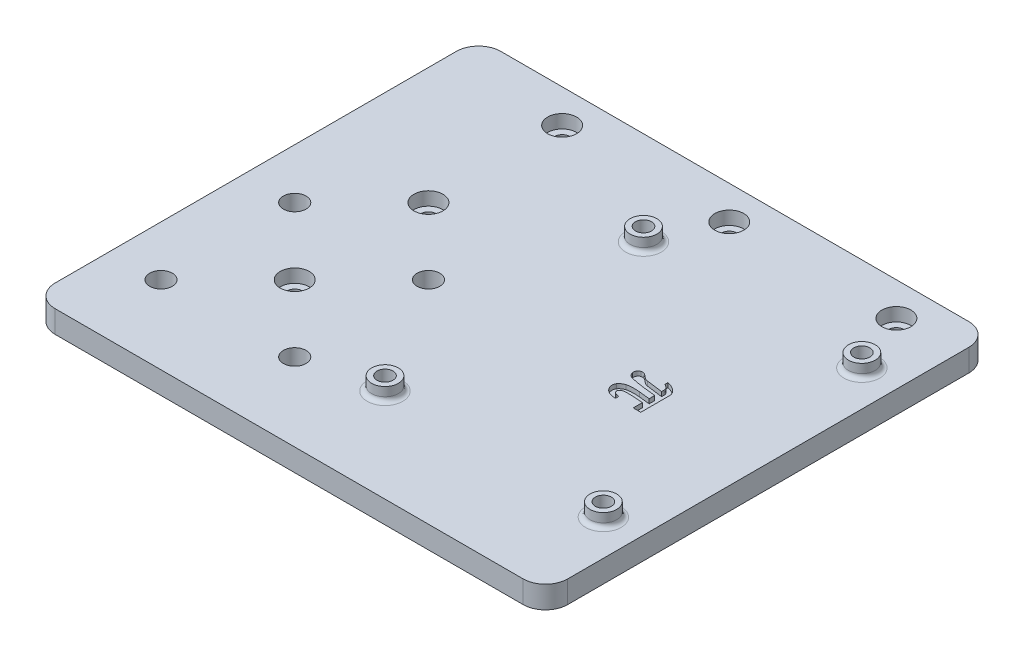
SolidWorks part; units mm, degrees
ref_plane "Front Plane" through (0, 0, 0) normal (0, 0, 1) x (1, 0, 0)
ref_plane "Top Plane" through (0, 0, 0) normal (0, 1, 0) x (1, 0, 0)
ref_plane "Right Plane" through (0, 0, 0) normal (1, 0, 0) x (0, 0, -1)
sketch "Sketch1" plane through (0, 0, 0) normal (0, 1, 0) x (1, 0, 0)
  line L1 (0, 0) -> (65, 0)
  line L2 (0, 0) -> (0, -100)
  line L3 (0, -100) -> (65, -100)
  line L4 (65, 0) -> (65, -100)
  dimension "D1" = 65
  dimension "D2" = 100
extrude "Boss-Extrude1" add sketch "Sketch1" along normal blind 5
sketch "Sketch2" plane through (0, 5, 0) normal (0, 1, 0) x (1, 0, 0)
  line L0 (32.5, 0) -> (32.5, -13.391) construction
  line L1 (8, -21) -> (57, -21) construction
  line L2 (8, -21) -> (8, -79) construction
  line L3 (8, -79) -> (57, -79) construction
  line L4 (57, -21) -> (57, -79) construction
  line L5 (65, 0) -> (0, 0) construction
  line L6 (32.5, -21) -> (32.5, -41.8005) construction
  line L7 (0, -50) -> (9.0135, -50) construction
  line L8 (0, 0) -> (0, -100) construction
  circle A0 centre (8, -21) radius 3
  circle A1 centre (57, -21) radius 3
  circle A2 centre (57, -79) radius 3
  circle A3 centre (8, -79) radius 3
  point P11 (8, -21)
  point P12 (57, -21)
  point P13 (57, -79)
  point P14 (8, -79)
  point P19 (8, -50)
  dimension "D3" = 6
  dimension "D1" = 58
  dimension "D2" = 49
extrude "Boss-Extrude2" add sketch "Sketch2" along normal blind 3
sketch "Sketch3" plane through (0, 8, 0) normal (0, 1, 0) x (1, 0, 0)
  point P0 (8, -21)
  point P1 (57, -21)
  point P3 (57, -79)
  point P5 (8, -79)
hole_wizard "Ø3.6 (3.6) Diameter Hole1" positions "Sketch3" profile "Sketch4" hole size "Ø3.6" standard "ANSI Metric" end condition up to next
sketch "Sketch4" plane through (8, 8, 21) normal (1, 0, 0) x (0, 0, 1)
  line L0 (0, 0) -> (0, 8)
  line L1 (0, 8) -> (1.8, 8)
  line L2 (1.8, 8) -> (1.8, 0)
  line L5 (1.8, 0) -> (0, 0)
  line L11 (0, -6.35) -> (0, 107.95) construction
  dimension "Thru Hole Dia." = 3.6
  dimension "Thru Hole Depth" = 8
chamfer "Chamfer1" [suppressed] distance 0.5 angle 45
sketch "Sketch5" plane through (0, 5, 0) normal (0, 1, 0) x (1, 0, 0)
  line L0 (32.5, 0) -> (32.5, -29.0521) construction
  line L1 (65, 0) -> (0, 0) construction
  line L2 (13.75, -7.5) -> (51.25, -7.5) construction
  point P7 (32.5, -7.5)
  dimension "D1" = 7.5
  dimension "D2" = 37.5
hole_wizard "CBORE for M3 SHCS1" positions "Sketch8" profile "Sketch7" counterbore size "M3" standard "ANSI Metric" end condition up to next
sketch "Sketch8" plane through (0, 5, 0) normal (0, 1, 0) x (1, 0, 0)
  point P0 (13.75, -7.5)
  point P3 (51.25, -7.5)
sketch "Sketch7" plane through (13.75, 5, 7.5) normal (1, 0, 0) x (0, 0, 1)
  line L0 (0, 0) -> (0, 5)
  line L1 (0, 5) -> (1.7, 5)
  line L3 (1.7, 5) -> (1.7, 3)
  line L4 (1.7, 3) -> (3.25, 3)
  line L5 (3.25, 3) -> (3.25, 0)
  line L7 (3.25, 0) -> (0, 0)
  line L11 (0, -6.35) -> (0, 107.95) construction
  dimension "Thru Hole Dia." = 3.4
  dimension "Thru Hole Depth" = 5
  dimension "C'Bore Dia." = 6.5
  dimension "C'Bore Depth" = 3
sketch "Sketch9" plane through (0, 0, 0) normal (-1, 0, 0) x (0, 0, 1)
  line L0 (0, 0) -> (100, 0) construction
  line L1 (0, 5) -> (100, 5)
  line L2 (0, 5) -> (0, 0)
  line L3 (0, 0) -> (100, 0)
  line L4 (100, 5) -> (100, 0)
  dimension "D1" = 100
extrude "Boss-Extrude3" add sketch "Sketch9" along normal blind 50
sketch "Sketch11" plane through (0, 5, 0) normal (0, 1, 0) x (1, 0, 0)
  line L0 (13.75, -7.5) -> (-50, -7.5) construction
  line L1 (-50, -100) -> (-50, 0) construction
  line L4 (-23.75, -7.5) -> (-23.75, -37.5) construction
  line L7 (-23.75, -37.5) -> (-23.75, -67.5) construction
  point P6 (-23.75, -7.5)
  point P20 (-23.75, -37.5)
  point P29 (-23.75, -67.5)
  dimension "D1" = 37.5
  dimension "D2" = 30
  dimension "D3" = 30
hole_wizard "CBORE for M3 SHCS2" positions "Sketch11" profile "Sketch12" counterbore size "M3" standard "ANSI Metric" end condition up to next
sketch "Sketch12" plane through (-23.75, 5, 67.5) normal (1, 0, 0) x (0, 0, 1)
  line L0 (0, 0) -> (0, 5)
  line L1 (0, 5) -> (1.7, 5)
  line L3 (1.7, 5) -> (1.7, 3)
  line L4 (1.7, 3) -> (3.25, 3)
  line L5 (3.25, 3) -> (3.25, 0)
  line L7 (3.25, 0) -> (0, 0)
  line L11 (0, -6.35) -> (0, 107.95) construction
  dimension "Thru Hole Dia." = 3.4
  dimension "Thru Hole Depth" = 5
  dimension "C'Bore Dia." = 6.5
  dimension "C'Bore Depth" = 3
sketch "Sketch16" plane through (0, 5, 0) normal (0, 1, 0) x (1, 0, 0)
  line L0 (8, -21) -> (57, -21) construction
  line L1 (8, -79) -> (57, -79) construction
  line L2 (32.5, -21) -> (32.5, -79) construction
  text T0 "<b>π</b>\r\n" font "Arial Rounded MT Bold" height in points 48
extrude "Cut-Extrude1" cut sketch "Sketch16" against normal blind 1
fillet "Fillet1" radius 1 4 edges at (8, 5, 82) (8, 5, 24) (57, 5, 24) (57, 5, 82)
fillet "Fillet2" radius 5 4 edges at (65, 2.5, 100) (65, 2.5, 0) (-50, 2.5, 0) (-50, 2.5, 100)
sketch "Sketch17" plane through (0, 5, 0) normal (0, 1, 0) x (1, 0, 0)
  line L0 (-23.75, -7.5) -> (-23.75, -47.7865) construction
  line L1 (-38.75, -52.5) -> (-8.75, -52.5) construction
  line L2 (-38.75, -52.5) -> (-38.75, -82.5) construction
  line L3 (-38.75, -82.5) -> (-8.75, -82.5) construction
  line L4 (-8.75, -52.5) -> (-8.75, -82.5) construction
  line L5 (-25.45, -67.5) -> (-33.69, -67.5) construction
  circle A2 centre (-23.75, -67.5) radius 1.7 construction
  point P8 (-23.75, -52.5)
  point P9 (-38.75, -67.5)
  point P16 (-8.75, -52.5)
  point P17 (-38.75, -52.5)
  point P18 (-8.75, -82.5)
  point P19 (-38.75, -82.5)
  dimension "D1" = 30
hole_wizard "Ø5.1 (5.1) Diameter Hole1" positions "Sketch17" profile "Sketch18" hole size "Ø5.1" standard "ANSI Metric"
sketch "Sketch18" plane through (-38.75, 5, 82.5) normal (1, 0, 0) x (0, 0, 1)
  line L0 (0, 0) -> (0, 5)
  line L1 (0, 5) -> (2.55, 5)
  line L2 (2.55, 5) -> (2.55, 0)
  line L5 (2.55, 0) -> (0, 0)
  line L11 (0, -6.35) -> (0, 107.95) construction
  dimension "Thru Hole Dia." = 5.1
  dimension "Thru Hole Depth" = 5
